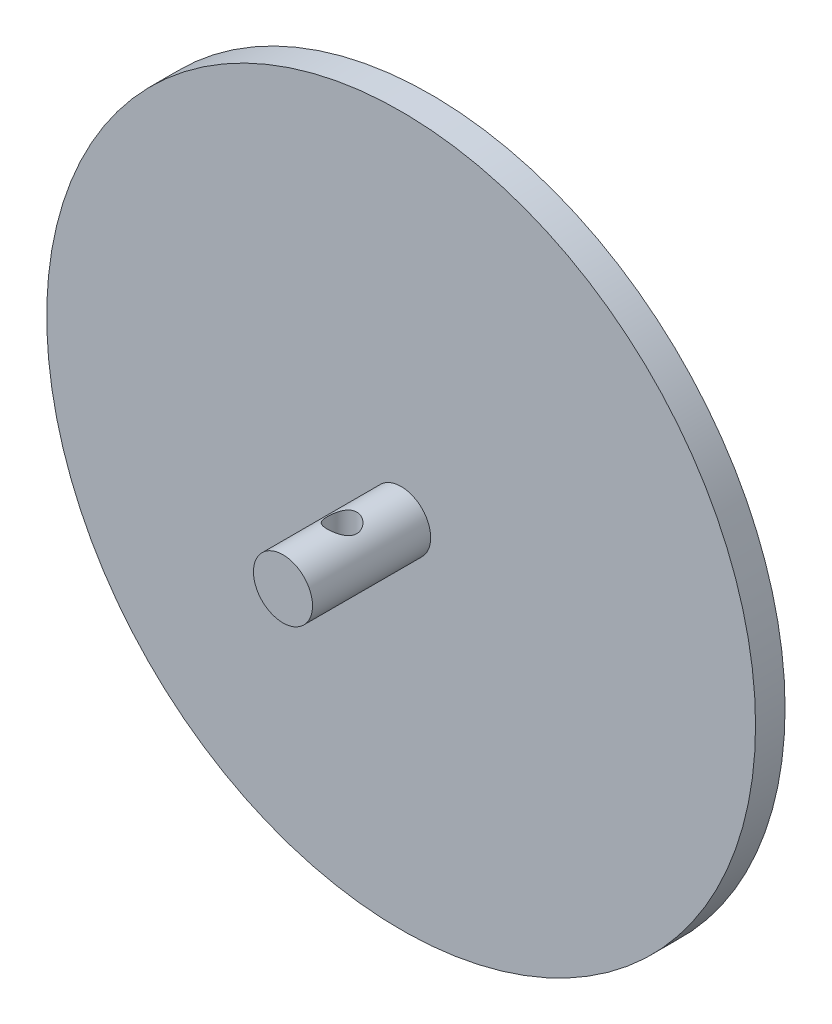
SolidWorks part; units mm, degrees
material "Nickel"
ref_plane "Front" through (0, 0, 0) normal (0, 0, 1) x (1, 0, 0)
ref_plane "Top" through (0, 0, 0) normal (0, 1, 0) x (1, 0, 0)
ref_plane "Right" through (0, 0, 0) normal (1, 0, 0) x (0, 0, -1)
sketch "Sketch2" plane through (0, 0, 0) normal (0, 0, 1) x (1, 0, 0)
  circle A0 centre (0, 0) radius 6.35
  dimension "D1" = 12.7
extrude "Boss-Extrude1" add sketch "Sketch2" along normal blind 25.4
sketch "Sketch3" plane through (0, 0, 0) normal (0, 1, 0) x (1, 0, 0)
  circle A0 centre (0, -12.7) radius 3.175
  dimension "D2" = 6.35
  dimension "D1" = 12.7
extrude "Cut-Extrude1" cut sketch "Sketch3" against normal through all both and the other way through all
ref_axis "Axis1" through (0, 0, 50) along (0, 0, -1)
sketch "Sketch7" plane through (0, 0, 0) normal (0, 1, 0) x (1, 0, 0)
  line L0 (-69.85, 6.35) -> (-76.2, 6.35)
  line L1 (-76.2, 6.35) -> (-76.2, 0)
  line L2 (-76.2, 0) -> (0, 0)
  line L6 (0, 0) -> (0, 3.175)
  arc A0 (-69.85, 6.35) -> (0, 3.175) centre (0, 773.1125) ccw
  dimension "D5" = 6.35
  dimension "D1" = 6.35
revolve "Revolve2" add sketch "Sketch7" angle 360 about axis through (0, 0, 50) along (0, 0, -1)
